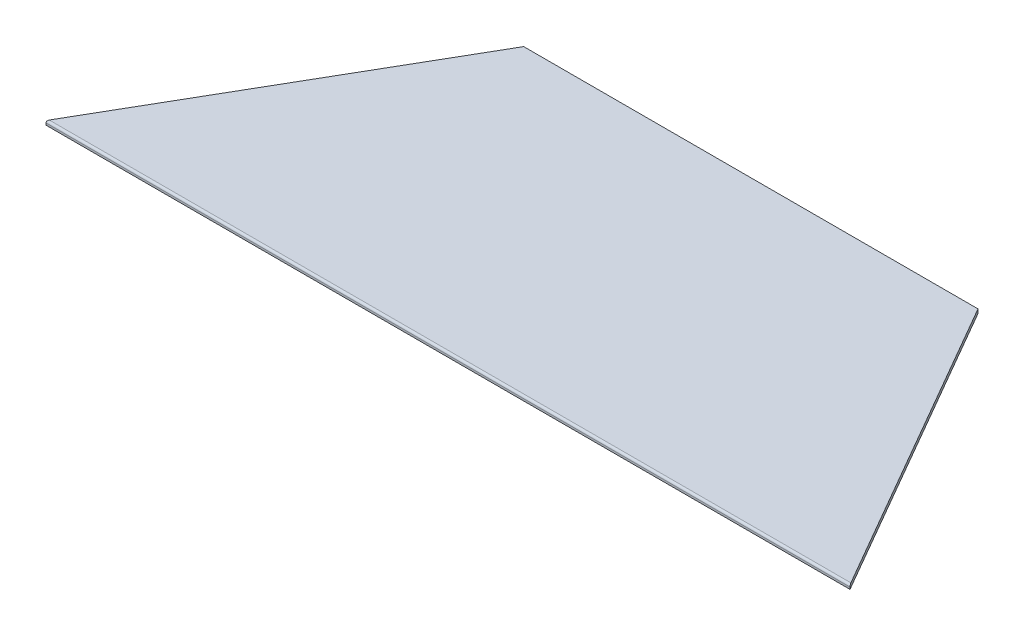
SolidWorks part; units mm, degrees
ref_plane "Front Plane" through (0, 0, 0) normal (0, 0, 1) x (1, 0, 0)
ref_plane "Top Plane" through (0, 0, 0) normal (0, 1, 0) x (1, 0, 0)
ref_plane "Right Plane" through (0, 0, 0) normal (1, 0, 0) x (0, 0, -1)
sketch "Sketch1" plane through (0, 0, 0) normal (0, 1, 0) x (1, 0, 0)
  line L0 (202.2882, 0) -> (202.2882, 166.1709) construction
  line L1 (0, 0) -> (404.5764, 0)
  line L3 (87.9882, 152.4) -> (316.5882, 152.4)
  line L5 (202.2882, 166.1709) -> (316.5882, 152.4) construction
  line L6 (202.2882, 166.1709) -> (87.9882, 152.4) construction
  line L7 (87.9882, 152.4) -> (0, 0)
  line L8 (316.5882, 152.4) -> (404.5764, 0)
  dimension "D1" = 60
  dimension "D2" = 228.6
  dimension "D3" = 152.4
  dimension "D4" = 60
extrude "Boss-Extrude1" add sketch "Sketch1" along normal blind 2.0574
fillet "Fillet1" radius 1.0287 1 edges at (202.2882, 2.0574, 0)
